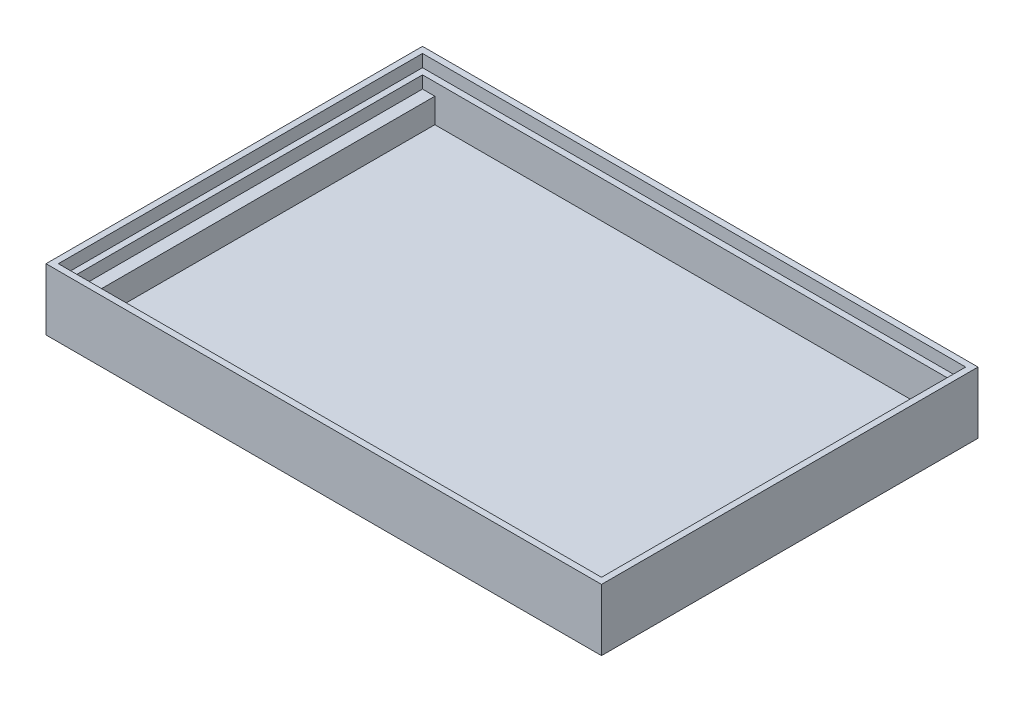
SolidWorks part; units mm, degrees
ref_plane "Front Plane" through (0, 0, 0) normal (0, 0, 1) x (1, 0, 0)
ref_plane "Top Plane" through (0, 0, 0) normal (0, 1, 0) x (1, 0, 0)
ref_plane "Right Plane" through (0, 0, 0) normal (1, 0, 0) x (0, 0, -1)
sketch "Sketch1" plane through (0, 0, 0) normal (0, 1, 0) x (1, 0, 0)
  line L0 (0, 0) -> (90, 0)
  line L1 (90, 0) -> (90, 61)
  line L2 (90, 61) -> (0, 61)
  line L3 (0, 61) -> (0, 0)
  dimension "D1" = 90
  dimension "D2" = 61
extrude "Boss-Extrude1" add sketch "Sketch1" along normal blind 2
sketch "Sketch2" plane through (0, 2, 0) normal (0, 1, 0) x (1, 0, 0)
  line L0 (90, 61) -> (0, 61) construction
  line L1 (0, 61) -> (0, 0) construction
  line L2 (0, 0) -> (90, 0) construction
  line L3 (90, 0) -> (90, 61) construction
  line L4 (90, 61) -> (0, 61)
  line L5 (0, 61) -> (0, 0)
  line L6 (0, 0) -> (90, 0)
  line L7 (90, 0) -> (90, 61)
  line L8 (88, 59) -> (2, 59)
  line L9 (2, 59) -> (2, 2)
  line L10 (2, 2) -> (88, 2)
  line L11 (88, 2) -> (88, 59)
  dimension "D1" = 2
extrude "Boss-Extrude2" add sketch "Sketch2" along normal blind 8
sketch "Sketch3" plane through (0, 2, 0) normal (0, 1, 0) x (1, 0, 0)
  line L0 (83, 2) -> (83, 9)
  line L2 (2, 2) -> (88, 2) construction
  line L3 (83, 9) -> (57, 9)
  line L5 (57, 9) -> (57, 2)
  line L7 (57, 2) -> (83, 2)
  line L8 (88, 2) -> (88, 59) construction
  dimension "D1" = 7
  dimension "D2" = 5
  dimension "D3" = 26
extrude "Cut-Extrude1" cut sketch "Sketch3" against normal blind 2
sketch "Sketch4" plane through (0, 2, 0) normal (0, 1, 0) x (1, 0, 0)
  line L0 (2, 59) -> (4, 59)
  line L1 (88, 59) -> (2, 59) construction
  line L2 (4, 59) -> (4, 2)
  line L3 (2, 2) -> (88, 2) construction
  line L4 (4, 2) -> (2, 2)
  line L5 (2, 2) -> (2, 59)
  line L6 (88, 59) -> (86, 59)
  line L7 (86, 59) -> (86, 2)
  line L8 (2, 2) -> (57, 2) construction
  line L9 (86, 2) -> (88, 2)
  line L10 (88, 2) -> (88, 59)
  dimension "D1" = 2
  dimension "D2" = 2
extrude "Boss-Extrude3" add sketch "Sketch4" along normal blind 4
sketch "Sketch5" plane through (0, 10, 0) normal (0, 1, 0) x (1, 0, 0)
  line L0 (88, 59) -> (2, 59) construction
  line L1 (2, 59) -> (2, 2) construction
  line L2 (2, 2) -> (88, 2) construction
  line L3 (88, 2) -> (88, 59) construction
  line L4 (88, 59) -> (2, 59)
  line L5 (2, 59) -> (2, 2)
  line L6 (2, 2) -> (88, 2)
  line L7 (88, 2) -> (88, 59)
  line L8 (89, 60) -> (1, 60)
  line L9 (1, 60) -> (1, 1)
  line L10 (1, 1) -> (89, 1)
  line L11 (89, 1) -> (89, 60)
  dimension "D1" = 1
extrude "Cut-Extrude2" cut sketch "Sketch5" against normal blind 2
